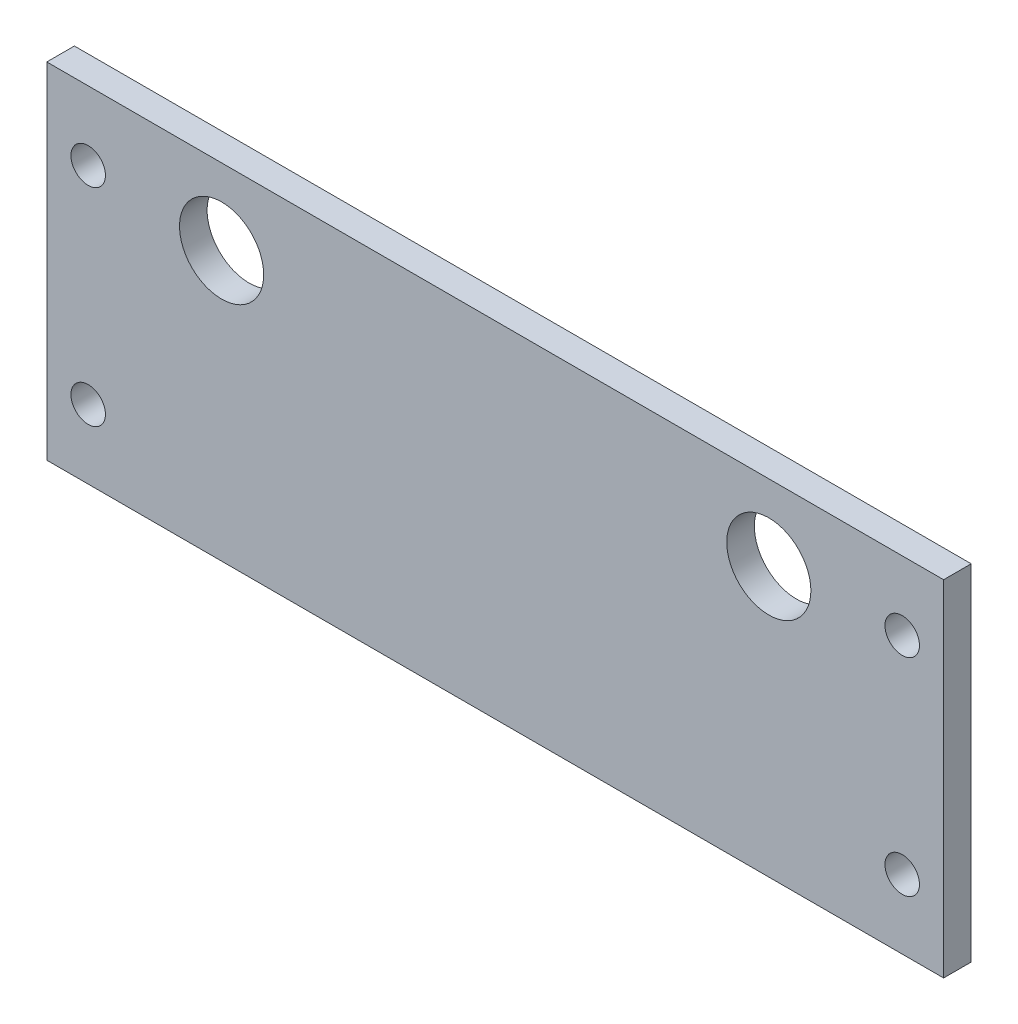
SolidWorks part; units mm, degrees
ref_plane "正面" through (0, 0, 0) normal (0, 0, 1) x (1, 0, 0)
ref_plane "平面" through (0, 0, 0) normal (0, 1, 0) x (1, 0, 0)
ref_plane "右側面" through (0, 0, 0) normal (1, 0, 0) x (0, 0, -1)
sketch "ｽｹｯﾁ1" plane through (0, 0, 0) normal (0, 0, 1) x (1, 0, 0)
  line L0 (0, 0) -> (0, 7)
  line L1 (-32.5, 12.5) -> (32.5, 12.5)
  line L2 (-32.5, 12.5) -> (-32.5, -12.5)
  line L3 (-32.5, -12.5) -> (32.5, -12.5)
  line L4 (32.5, 12.5) -> (32.5, -12.5)
  line L5 (-32.5, 12.5) -> (32.5, -12.5) construction
  line L6 (-32.5, -12.5) -> (32.5, 12.5) construction
  line L7 (0, 7) -> (19.83, 7)
  line L8 (0, 7) -> (-19.83, 7)
  circle A0 centre (-19.83, 7) radius 3.05
  circle A1 centre (19.83, 7) radius 3.05
  point P0 (0, 0)
  dimension "D3" = 6.1
  dimension "D4" = 6.1
  dimension "D1" = 19.83
  dimension "D2" = 19.83
  dimension "D5" = 25
  dimension "D6" = 65
  dimension "D7" = 7
extrude "ﾎﾞｽ - 押し出し1" add sketch "ｽｹｯﾁ1" along normal blind 2
sketch "ｽｹｯﾁ2" plane through (0, 0, 2) normal (0, 0, 1) x (1, 0, 0)
  line L0 (-32.5, 12.5) -> (-32.5, -12.5) construction
  line L1 (-32.5, 12.5) -> (-29.5, 12.5)
  line L2 (-32.5, 12.5) -> (-32.5, 7.5)
  line L3 (-32.5, 7.5) -> (-29.5, 7.5)
  line L4 (-29.5, 12.5) -> (-29.5, 7.5)
  line L5 (-32.5, -12.5) -> (-29.5, -12.5)
  line L6 (-32.5, -12.5) -> (-32.5, -7.5)
  line L7 (-32.5, -7.5) -> (-29.5, -7.5)
  line L8 (-29.5, -12.5) -> (-29.5, -7.5)
  line L9 (-32.5, -12.5) -> (32.5, -12.5) construction
  line L10 (32.5, 12.5) -> (32.5, -12.5) construction
  line L11 (32.5, -12.5) -> (29.5, -12.5)
  line L12 (32.5, -12.5) -> (32.5, -7.5)
  line L13 (32.5, -7.5) -> (29.5, -7.5)
  line L14 (29.5, -12.5) -> (29.5, -7.5)
  line L16 (32.5, 12.5) -> (29.5, 12.5)
  line L17 (32.5, 12.5) -> (32.5, 7.5)
  line L18 (32.5, 7.5) -> (29.5, 7.5)
  line L19 (29.5, 12.5) -> (29.5, 7.5)
  circle A0 centre (-29.5, 7.5) radius 1.6
  circle A1 centre (-29.5, -7.5) radius 1.6
  circle A2 centre (29.5, 7.5) radius 1.6
  circle A3 centre (29.5, -7.5) radius 1.6
  dimension "D9" = 3.2
  dimension "D10" = 3.2
  dimension "D11" = 3.2
  dimension "D12" = 3.2
  dimension "D1" = 3
  dimension "D2" = 5
  dimension "D3" = 3
  dimension "D4" = 5
  dimension "D5" = 3
  dimension "D6" = 5
  dimension "D7" = 3
  dimension "D8" = 5
hole_wizard "M3x0.5 ねじ穴1" positions "3Dｽｹｯﾁ2" profile "ｽｹｯﾁ4" tap size "M3x0.5" standard "JIS"
sketch3d "3Dｽｹｯﾁ2"
  point P0 (-29.5, 7.5, 2)
  point P3 (-29.5, -7.5, 2)
  point P6 (29.5, 7.5, 2)
  point P9 (29.5, -7.5, 2)
sketch "ｽｹｯﾁ4" plane through (-29.5, 7.5, 2) normal (1, 0, 0) x (0, -1, 0)
  line L0 (0, 0) -> (0, 9.2511)
  line L1 (0, 9.2511) -> (1.25, 8.5)
  line L2 (1.25, 8.5) -> (1.25, 0)
  line L5 (1.25, 0) -> (0, 0)
  line L10 (0, 9.2511) -> (-1.25, 8.5) construction
  line L11 (0, -6.35) -> (0, 107.95) construction
  dimension "ねじ下穴ﾄﾞﾘﾙ直径" = 2.5
  dimension "ねじ下穴ﾄﾞﾘﾙの深さ" = 8.5
  dimension "ﾄﾞﾘﾙ角度" = 118
cosmetic thread "穴のねじ山1" parameters "D1"=3, "D2"=3
cosmetic thread "穴のねじ山2" parameters "D1"=3, "D2"=3
cosmetic thread "穴のねじ山3" parameters "D1"=3, "D2"=3
cosmetic thread "穴のねじ山4" parameters "D1"=3, "D2"=3
